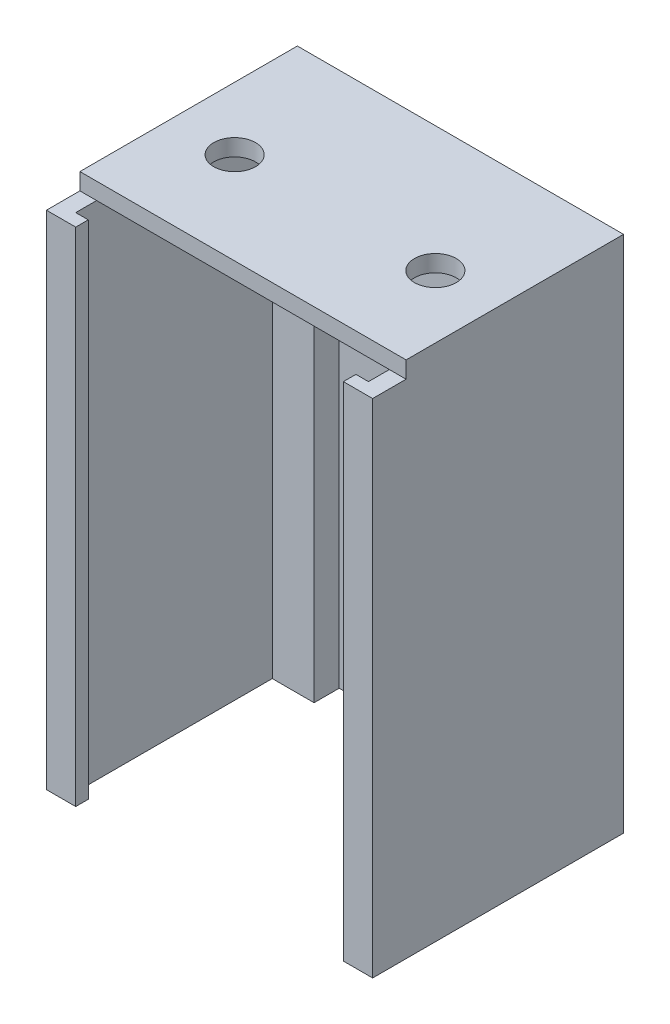
SolidWorks part; units mm, degrees
ref_plane "Plan de face" through (0, 0, 0) normal (0, 0, 1) x (1, 0, 0)
ref_plane "Plan de dessus" through (0, 0, 0) normal (0, 1, 0) x (1, 0, 0)
ref_plane "Plan de droite" through (0, 0, 0) normal (1, 0, 0) x (0, 0, -1)
sketch "Esquisse1" plane through (0, 0, 0) normal (0, 1, 0) x (1, 0, 0)
  line L0 (152.6773, 0) -> (0, 0) construction
  line L1 (0, 0) -> (0, 96.7963) construction
  line L2 (71, -60) -> (78, -60)
  line L3 (0, 0) -> (78, 0)
  line L4 (0, 0) -> (0, -60)
  line L6 (78, 0) -> (78, -60)
  line L9 (14, -4) -> (64, -4)
  line L11 (39, 0) -> (39, -168.7894) construction
  line L28 (74, -57) -> (74, -10)
  line L30 (4, -57) -> (4, -10)
  line L31 (71, -60) -> (71, -57)
  line L32 (71, -57) -> (74, -57)
  line L33 (7, -60) -> (0, -60)
  line L34 (7, -60) -> (7, -57)
  line L35 (7, -57) -> (4, -57)
  line L36 (4, -10) -> (14, -10)
  line L39 (74, -10) -> (64, -10)
  line L40 (64, -4) -> (64, -10)
  line L41 (14, -4) -> (14, -10)
  dimension "D1" = 60
  dimension "D2" = 78
  dimension "D3" = 47
  dimension "D4" = 7
  dimension "D5" = 4
  dimension "D6" = 3
  dimension "D7" = 3
  dimension "D8" = 14
  dimension "D9" = 10
extrude "Boss.-Extru.2" add sketch "Esquisse1" along normal blind 120
sketch "Esquisse2" plane through (0, 0, 0) normal (0, -1, 0) x (1, 0, 0)
  line L0 (78, 0) -> (0, 0) construction
  line L1 (78, 60) -> (78, 0) construction
  line L2 (113.3263, 0) -> (0, 0) construction
  line L3 (0, 0) -> (0, 78.4952) construction
  circle A0 centre (69, 5) radius 2.25
  circle A1 centre (9, 5) radius 2.25
  dimension "D1" = 4.5
  dimension "D5" = 4.5
  dimension "D2" = 5
  dimension "D3" = 9
  dimension "D4" = 5
  dimension "D6" = 9
extrude "Enlèv. mat.-Extru.1" cut sketch "Esquisse2" against normal blind 5
sketch "Esquisse4" plane through (0, 120, 0) normal (0, 1, 0) x (1, 0, 0)
  line L0 (0, -52) -> (78, -52)
  line L1 (0, 0) -> (78, 0)
  line L2 (0, 0) -> (0, -52)
  line L4 (78, 0) -> (78, -52)
  line L5 (0, -60) -> (7, -60) construction
  dimension "D1" = 8
extrude "Boss.-Extru.3" add sketch "Esquisse4" along normal blind 4
sketch "Esquisse6" plane through (0, 124, 0) normal (0, 1, 0) x (1, 0, 0)
  line L0 (78, 0) -> (0, 0) construction
  line L1 (0, 0) -> (0, -52) construction
  line L2 (78, -52) -> (78, 0) construction
  circle A0 centre (15, -30) radius 5
  circle A1 centre (63, -30) radius 5
  dimension "D1" = 10
  dimension "D2" = 10
  dimension "D3" = 30
  dimension "D4" = 30
  dimension "D5" = 15
  dimension "D6" = 15
extrude "Enlèv. mat.-Extru.3" cut sketch "Esquisse6" against normal blind 10
